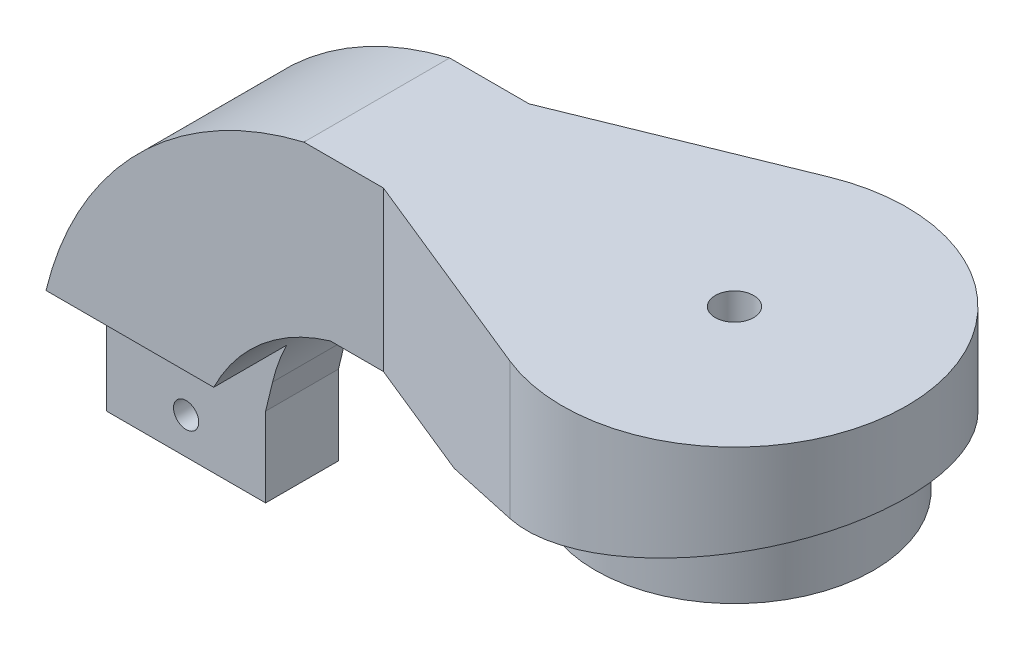
SolidWorks part; units mm, degrees
ref_plane "Front" through (0, 0, 0) normal (0, 0, 1) x (1, 0, 0)
ref_plane "Top" through (0, 0, 0) normal (0, 1, 0) x (1, 0, 0)
ref_plane "Right" through (0, 0, 0) normal (1, 0, 0) x (0, 0, -1)
sketch "Sketch1" plane through (0, 0, 0) normal (0, 1, 0) x (1, 0, 0)
  line L0 (0, 0) -> (-42, 0) construction
  line L1 (-42, 0) -> (-42, 11)
  line L2 (-42, 0) -> (-42, -11)
  line L3 (-42, 11) -> (-9.7865, 24.0878)
  line L4 (-42, -11) -> (-9.7865, -24.0878)
  arc A0 (-9.7865, -24.0878) -> (-9.7865, 24.0878) centre (0, 0) ccw
  dimension "D1" = 52
  dimension "D2" = 42
  dimension "D3" = 11
  dimension "D4" = 11
extrude "Boss-Extrude1" add sketch "Sketch1" along normal blind 24
sketch "Sketch2" plane through (0, 0, 0) normal (0, 0, 1) x (1, 0, 0)
  line L0 (-24, 0) -> (26, 12)
  line L1 (-42, 0) -> (-9.7865, 0) construction
  line L2 (26, 0) -> (26, 24) construction
  line L3 (26, 12) -> (26, 0)
  line L4 (26, 0) -> (-24, 0)
  dimension "D1" = 12
  dimension "D2" = 50
extrude "Cut-Extrude1" cut sketch "Sketch2" against normal mid plane 59
sketch "Sketch3" plane through (0, 24, 0) normal (0, 1, 0) x (1, 0, 0)
  circle A0 centre (0, 0) radius 21
  dimension "D1" = 42
extrude "Boss-Extrude2" add sketch "Sketch3" against normal blind 24
sketch "Sketch4" plane through (0, 0, 0) normal (0, -1, 0) x (1, 0, 0)
  line L1 (2.829, 4.9) -> (-2.829, 4.9)
  line L2 (-2.829, 4.9) -> (-5.658, 0)
  line L3 (-5.658, 0) -> (-2.829, -4.9)
  line L4 (-2.829, -4.9) -> (2.829, -4.9)
  line L5 (2.829, -4.9) -> (5.658, 0)
  line L6 (5.658, 0) -> (2.829, 4.9)
  circle A0 centre (0, 0) radius 4.9 construction
  dimension "D1" = 9.8
extrude "Cut-Extrude2" cut sketch "Sketch4" against normal blind 4
sketch "Sketch5" plane through (0, 0, 0) normal (0, 0, 1) x (1, 0, 0)
  line L0 (-42, 24) -> (-9.7865, 24) construction
  line L1 (-42, 24) -> (-9.7865, 24)
  line L2 (-92.9418, -14.8696) -> (-94.7865, -22.5)
  line L3 (-69.7389, -20.7418) -> (-70.7865, -25.0753)
  line L4 (-42, 0) -> (-42, 24)
  line L5 (-9.7865, 24) -> (-9.7865, -71) construction
  line L6 (-97.7865, -99.5) -> (-9.7865, -99.5)
  line L7 (-97.7865, -99.5) -> (-97.7865, -56.5)
  line L8 (-97.7865, -56.5) -> (-9.7865, -56.5)
  line L9 (-9.7865, -99.5) -> (-9.7865, -56.5)
  line L10 (-97.7865, -99.5) -> (-9.7865, -56.5) construction
  line L11 (-97.7865, -56.5) -> (-9.7865, -99.5) construction
  line L12 (-97.7865, -71) -> (-9.7865, -71) construction
  line L13 (1.2135, -74) -> (1.2135, -68) construction
  line L14 (-9.7865, -68) -> (12.2135, -68)
  line L16 (-9.7865, -74) -> (12.2135, -74)
  line L17 (12.2135, -68) -> (12.2135, -74)
  line L18 (-9.7865, -71) -> (12.2135, -74) construction
  line L19 (-9.7865, -71) -> (12.2135, -68) construction
  line L20 (-41.2865, -136) -> (43.7135, -136)
  line L21 (-41.2865, -136) -> (-41.2865, -6)
  line L22 (-41.2865, -6) -> (43.7135, -6)
  line L23 (43.7135, -136) -> (43.7135, -6)
  line L24 (-41.2865, -136) -> (43.7135, -6) construction
  line L25 (-41.2865, -6) -> (43.7135, -136) construction
  line L26 (12.2135, -71) -> (1.2135, -71) construction
  line L27 (-94.7865, -22.5) -> (-94.7865, -37.0753)
  line L28 (-93.178, -46.5) -> (-90, -56.5)
  line L29 (-70.7865, -37.0753) -> (-94.7865, -37.0753)
  line L30 (-70.7865, -25.0753) -> (-70.7865, -37.0753)
  line L31 (-70.7865, -37.0753) -> (-63.178, -46.5)
  line L32 (-63.178, -46.5) -> (-42, -56.5)
  line L33 (-42, 24) -> (-54, 24)
  line L34 (-42, 0) -> (-50, 0)
  line L35 (-94.7865, -37.0753) -> (-93.178, -46.5)
  arc A2 (-69.7389, -20.7418) -> (-50, 0) centre (-41.8994, -27.4721) cw
  arc A4 (-92.9418, -14.8696) -> (-54, 24) centre (-41.7096, -27.2552) cw
  point P12 (-53.7865, -78)
  point P32 (1.2135, -71)
  dimension "D21" = 8
  dimension "D22" = 24
  dimension "D3" = 43
  dimension "D4" = 88
  dimension "D5" = 95
  dimension "D6" = 7
  dimension "D7" = 22
  dimension "D8" = 6
  dimension "D9" = 130
  dimension "D10" = 85
  dimension "D11" = 24
  dimension "D12" = 48
  dimension "D13" = 90
  dimension "D14" = 3
  dimension "D15" = 10
  dimension "D16" = 10
  dimension "D17" = 30
  dimension "D18" = 34
  dimension "D19" = 12
  dimension "D20" = 12
extrude "Boss-Extrude3" add sketch "Sketch5" along normal mid plane 22
sketch "Sketch6" plane through (0, 0, 0) normal (0, 0, 1) x (1, 0, 0)
  line L1 (-90, -56.5) -> (-42, -56.5) construction
  line L2 (-98, -99.5) -> (-9, -99.5)
  line L3 (-98, -99.5) -> (-98, -56.5)
  line L4 (-98, -56.5) -> (-9, -56.5)
  line L5 (-9, -99.5) -> (-9, -56.5)
  line L6 (-98, -99.5) -> (-9, -56.5) construction
  line L7 (-98, -56.5) -> (-9, -99.5) construction
  line L8 (-98, -78) -> (-9, -78)
  point P2 (-53.5, -78)
  dimension "D1" = 43
  dimension "D2" = 89
  dimension "D3" = 98
revolve "Revolve1" add sketch "Sketch6" angle 360 about L8
sketch "Sketch7" plane through (0, -56.5, 0) normal (0, -1, 0) x (1, 0, 0)
  line L4 (-90, -11) -> (-42, -11)
  line L5 (-42, -11) -> (-42, 11)
  line L6 (-42, 11) -> (-90, 11)
  line L7 (-90, 11) -> (-90, -11)
  line L8 (-90, -11) -> (-42, -11)
  line L9 (-42, -11) -> (-42, 11)
  line L10 (-42, 11) -> (-90, 11)
  line L11 (-90, 11) -> (-90, -11)
  dimension "D1" = 0
extrude "Boss-Extrude4" add sketch "Sketch7" along normal up to next
sketch "Sketch8" plane through (-98, 0, 0) normal (-1, 0, 0) x (0, 0, 1)
  circle A0 centre (0, -78) radius 18.5
  dimension "D1" = 37
extrude "Cut-Extrude3" cut sketch "Sketch8" against normal blind 83
sketch "Sketch9" plane through (-9, 0, 0) normal (1, 0, 0) x (0, 0, -1)
  line L0 (0, -78) -> (15.5, -78) construction
  circle A0 centre (15.5, -78) radius 1.6
  circle A1 centre (7.75, -91.4234) radius 1.6
  circle A2 centre (-7.75, -91.4234) radius 1.6
  circle A3 centre (-15.5, -78) radius 1.6
  circle A4 centre (-7.75, -64.5766) radius 1.6
  circle A5 centre (7.75, -64.5766) radius 1.6
  circle A6 centre (0, -85) radius 6.1
  point P16 (0, -78)
  dimension "D2" = 3.2
  dimension "D4" = 12.2
  dimension "D1" = 15.5
  dimension "D5" = 7
  dimension "D3" = 6
extrude "Cut-Extrude4" cut sketch "Sketch9" against normal up to next
sketch "Sketch10" plane through (0, 24, 0) normal (0, 1, 0) x (1, 0, 0)
  circle A0 centre (0, 0) radius 2.9
  dimension "D1" = 5.8
extrude "Cut-Extrude5" cut sketch "Sketch10" against normal up to next
ref_plane "Plane1" through (-108, 0, 0) normal (-1, 0, 0) x (0, 0, 1)
sketch "Sketch12" plane through (-108, 0, 0) normal (-1, 0, 0) x (0, 0, 1)
  line L0 (0, -14.8696) -> (0, -37.0753)
  line L1 (11, -14.8696) -> (-11, -14.8696) construction
  line L2 (11, -37.0753) -> (-11, -37.0753) construction
  line L3 (0, -37.0753) -> (-35.0099, -37.0753)
  line L4 (-35.0099, -37.0753) -> (-35.0099, -113.3346)
  line L5 (-35.0099, -113.3346) -> (34.5151, -113.3346)
  line L6 (34.5151, -113.3346) -> (34.5151, -14.8696)
  line L7 (34.5151, -14.8696) -> (0, -14.8696)
extrude "Cut-Extrude6" cut sketch "Sketch12" against normal up to next
sketch "Sketch13" plane through (0, 0, 0) normal (0, 0, 1) x (1, 0, 0)
  line L0 (-94.7865, -31.5753) -> (-70.7865, -31.5753) construction
  line L1 (-94.7865, -22.5) -> (-94.7865, -37.0753) construction
  line L2 (-70.7865, -25.0753) -> (-70.7865, -37.0753) construction
  line L3 (-94.2715, -20.3696) -> (-69.6489, -20.3696) construction
  line L5 (-92.9418, -14.8696) -> (-94.7865, -22.5) construction
  line L6 (-69.7389, -20.7418) -> (-70.7865, -25.0753) construction
  line L7 (-92.9418, -14.8696) -> (-67.6192, -14.8696) construction
  line L8 (-70.7865, -37.0753) -> (-94.7865, -37.0753) construction
  circle A1 centre (-81.9602, -20.3696) radius 1.9
  circle A2 centre (-82.7865, -31.5753) radius 1.9
  dimension "D3" = 3.8
  dimension "D4" = 3.8
  dimension "D1" = 5.5
  dimension "D2" = 5.5
extrude "Cut-Extrude7" cut sketch "Sketch13" against normal through all
